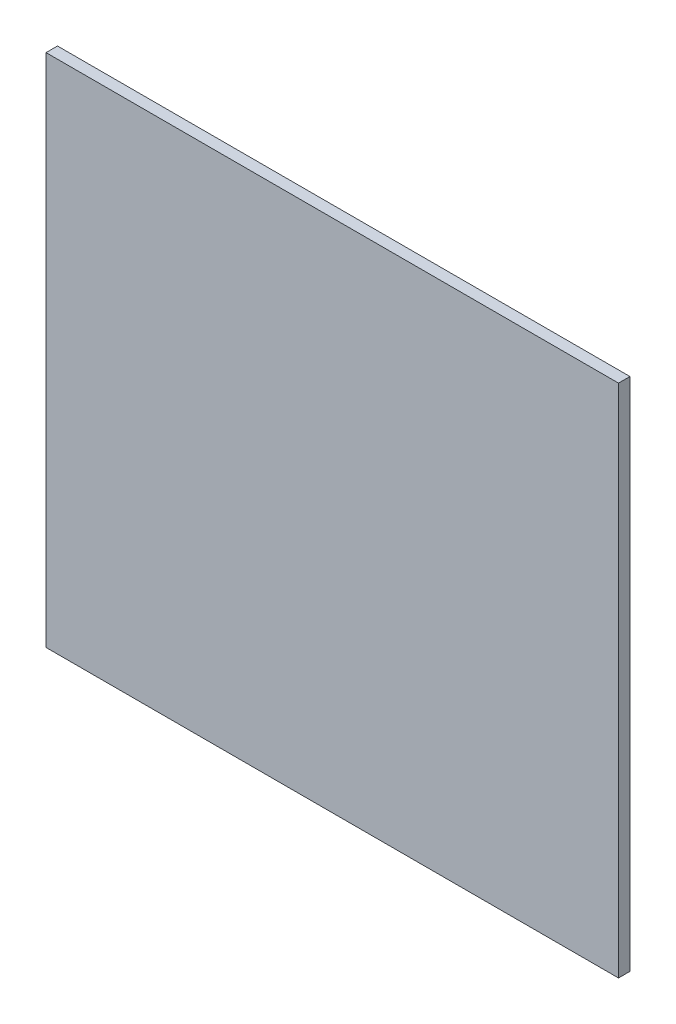
SolidWorks part; units mm, degrees
ref_plane "Ön Düzlem" through (0, 0, 0) normal (0, 0, 1) x (1, 0, 0)
ref_plane "Üst Düzlem" through (0, 0, 0) normal (0, 1, 0) x (1, 0, 0)
ref_plane "Sağ Düzlem" through (0, 0, 0) normal (1, 0, 0) x (0, 0, -1)
sketch "Sketch1" plane through (0, 0, 0) normal (0, 0, 1) x (1, 0, 0)
  line L1 (-250, -225) -> (250, -225)
  line L2 (-250, -225) -> (-250, 225)
  line L3 (-250, 225) -> (250, 225)
  line L4 (250, -225) -> (250, 225)
  line L5 (-250, -225) -> (250, 225) construction
  line L6 (-250, 225) -> (250, -225) construction
  point P0 (0, 0)
  dimension "D1" = 500
  dimension "D2" = 450
extrude "Boss-Extrude1" add sketch "Sketch1" along normal blind 10
